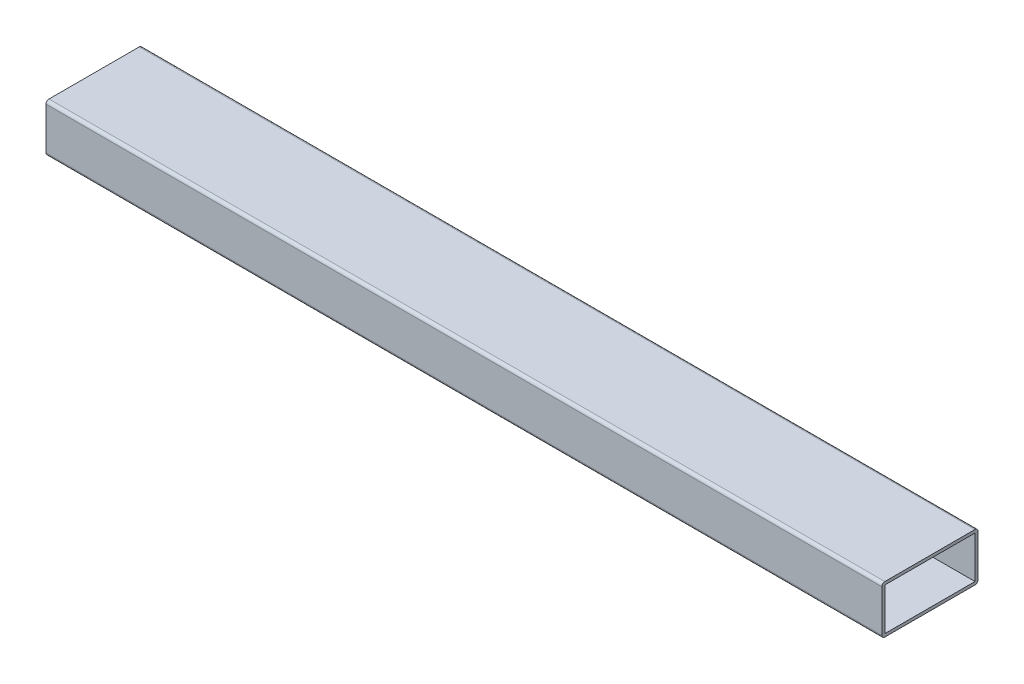
SolidWorks part; units mm, degrees
ref_plane "Front Plane" through (0, 0, 0) normal (0, 0, 1) x (1, 0, 0)
ref_plane "Top Plane" through (0, 0, 0) normal (0, 1, 0) x (1, 0, 0)
ref_plane "Right Plane" through (0, 0, 0) normal (1, 0, 0) x (0, 0, -1)
sketch "Sketch1" plane through (0, 0, 0) normal (1, 0, 0) x (0, 0, -1)
  line L1 (0, 0) -> (50.8, 0)
  line L2 (0, 0) -> (0, 25.4)
  line L3 (0, 25.4) -> (50.8, 25.4)
  line L4 (50.8, 0) -> (50.8, 25.4)
  dimension "D1" = 25.4
  dimension "D2" = 50.8
extrude "Boss-Extrude1" add sketch "Sketch1" along normal blind 441.45
sketch "Sketch2" plane through (0, 0, 0) normal (-1, 0, 0) x (0, 0, 1)
  line L0 (-50.8, 25.4) -> (-50.8, 23.8125)
  line L1 (-50.8, 0) -> (-50.8, 25.4) construction
  line L2 (-50.8, 23.8125) -> (-49.2125, 23.8125)
  line L3 (0, 0) -> (0, 1.5875)
  line L4 (0, 25.4) -> (0, 0) construction
  line L5 (0, 1.5875) -> (-1.5875, 1.5875)
  line L7 (-1.5875, 1.5875) -> (-49.2125, 1.5875)
  line L8 (-1.5875, 1.5875) -> (-1.5875, 23.8125)
  line L9 (-1.5875, 23.8125) -> (-49.2125, 23.8125)
  line L10 (-49.2125, 1.5875) -> (-49.2125, 23.8125)
  dimension "D1" = 1.5875
  dimension "D2" = 1.5875
  dimension "D3" = 1.5875
  dimension "D4" = 1.5875
extrude "Cut-Extrude1" cut sketch "Sketch2" against normal up to surface (441.45 mm away) contours L10 L7 L8 L9 up to face at (441.45, 12.7, -25.4)
fillet "Fillet1" radius 1.5875 4 edges at (220.725, 0, -50.8) (220.725, 0, 0) (220.725, 25.4, -50.8) (220.725, 25.4, 0)
